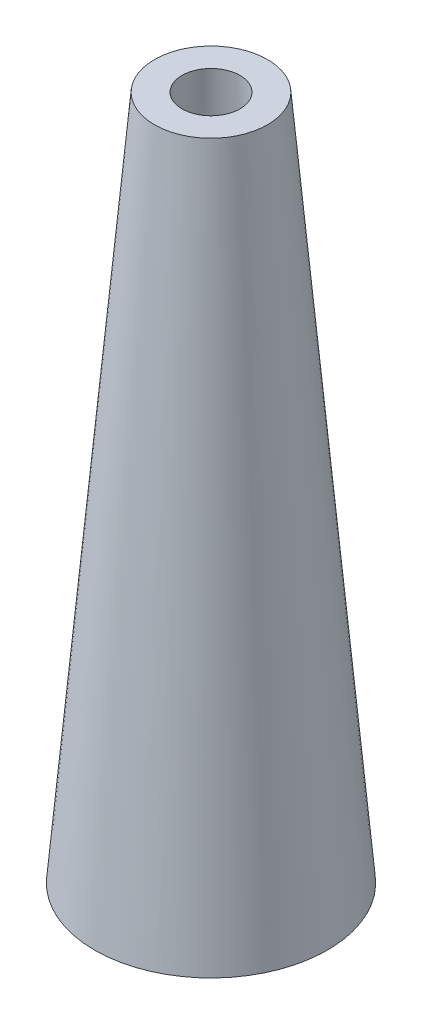
SolidWorks part; units mm, degrees
ref_plane "Front Plane" through (0, 0, 0) normal (0, 0, 1) x (1, 0, 0)
ref_plane "Top Plane" through (0, 0, 0) normal (0, 1, 0) x (1, 0, 0)
ref_plane "Right Plane" through (0, 0, 0) normal (1, 0, 0) x (0, 0, -1)
sketch "Çizim1" plane through (0, 0, 0) normal (0, 1, 0) x (1, 0, 0)
  circle A0 centre (0, 0) radius 1.7
extrude "Yükseklik-Ekstrüzyon1" add sketch "Çizim1" along normal blind 10 draft 5
sketch "Çizim2" plane through (0, 0, 0) normal (0, -1, 0) x (1, 0, 0)
  circle A0 centre (0, 0) radius 1.1228
extrude "Kes-Ekstrüzyon1" cut sketch "Çizim2" against normal blind 10 draft 4
sketch "Çizim3" plane through (0, 0, 0) normal (0, -1, 0) x (-1, 0, 0)
  line L0 (-1.1228, 0) -> (1.1228, 0) construction
  line L1 (0, 1.1228) -> (0, -1.1228) construction
  line L2 (0, 0) -> (-0.3536, 0.3536) construction
  line L3 (0, 0) -> (0.3536, 0.3536) construction
  line L4 (0, 0) -> (-0.3536, -0.3536) construction
  line L5 (0, 0) -> (0.3536, -0.3536) construction
  circle A0 centre (0, 0) radius 1.1228
  circle A1 centre (-0.3536, -0.3536) radius 0.1996
  circle A2 centre (-0.3536, 0.3536) radius 0.1968
  circle A3 centre (0.3536, 0.3536) radius 0.2032
  circle A4 centre (0.3536, -0.3536) radius 0.1971
extrude "Yükseklik-Ekstrüzyon3" add sketch "Çizim3" against normal blind 1
sketch "Çizim5" plane through (0, 0, 0) normal (0, -1, 0) x (1, 0, 0)
  line L0 (0, 0) -> (0, 0.8) construction
  circle A2 centre (0, 0.8) radius 0.2
  circle A3 centre (-0.8, 0) radius 0.2
  circle A4 centre (0, -0.8) radius 0.1977
  circle A5 centre (0.8, 0) radius 0.1977
extrude "Kes-Ekstrüzyon2" cut sketch "Çizim5" against normal blind 1 contours A5 | A3 | A4 | A2
sketch "Çizim6" plane through (0, 0, 0) normal (0, -1, 0) x (1, 0, 0)
  circle A0 centre (0, 0) radius 0.1967
extrude "Kes-Ekstrüzyon3" cut sketch "Çizim6" against normal blind 1
